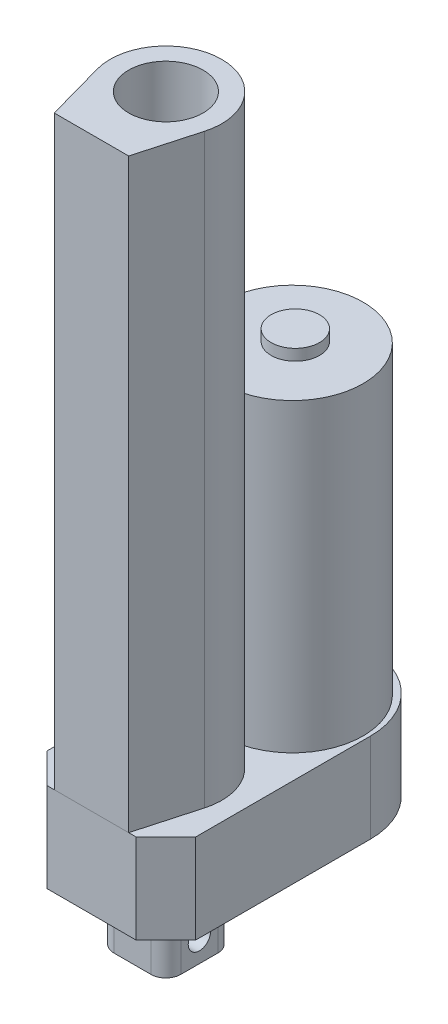
SolidWorks part; units mm, degrees
ref_plane "前视基准面" through (0, 0, 0) normal (0, 0, 1) x (1, 0, 0)
ref_plane "上视基准面" through (0, 0, 0) normal (0, 1, 0) x (1, 0, 0)
ref_plane "右视基准面" through (0, 0, 0) normal (1, 0, 0) x (0, 0, -1)
sketch "草图1" plane through (0, 0, 0) normal (0, 1, 0) x (1, 0, 0)
  line L0 (0, 8) -> (8, 0)
  line L1 (8, 0) -> (32, 0)
  line L2 (0, 8) -> (0, 55)
  line L4 (40, 8) -> (40, 55)
  line L5 (32, 0) -> (40, 8)
  arc A0 (40, 55) -> (0, 55) centre (20, 55) ccw
  point P0 (0, 0)
  point P4 (40, 0)
  dimension "D3" = 20
  dimension "D1" = 55
  dimension "D2" = 40
extrude "凸台-拉伸1" add sketch "草图1" along normal blind 24
sketch "草图2" plane through (0, 0, 0) normal (0, -1, 0) x (1, 0, 0)
  line L0 (8, 0) -> (32, 0) construction
  line L1 (15, -11) -> (25, -11)
  line L2 (11, -15) -> (11, -25)
  line L3 (15, -29) -> (25, -29)
  line L4 (29, -15) -> (29, -25)
  line L5 (0, -55) -> (0, -8) construction
  arc A0 (11, -25) -> (15, -29) centre (15, -25) ccw
  arc A1 (25, -29) -> (29, -25) centre (25, -25) ccw
  arc A2 (25, -11) -> (29, -15) centre (25, -15) cw
  arc A3 (15, -11) -> (11, -15) centre (15, -15) ccw
  point P12 (20, -29)
  dimension "D1" = 4
  dimension "D2" = 4
  dimension "D3" = 4
  dimension "D4" = 4
  dimension "D5" = 18
  dimension "D6" = 18
  dimension "D7" = 11
  dimension "D8" = 11
extrude "凸台-拉伸2" add sketch "草图2" along normal blind 17
sketch "草图3" plane through (29, 0, 0) normal (1, 0, 0) x (0, 0, -1)
  line L0 (25, -17) -> (15, -17) construction
  line L1 (8, 24) -> (55, 24) construction
  line L3 (11, -17) -> (11, 0) construction
  circle A0 centre (20, -11) radius 3
  dimension "D1" = 6
  dimension "D4" = 35
  dimension "D2" = 6
  dimension "D3" = 9
extrude "切除-拉伸1" cut sketch "草图3" against normal through all both and the other way through all
sketch "草图4" plane through (0, 24, 0) normal (0, 1, 0) x (1, 0, 0)
  line L0 (8, 0) -> (32, 0) construction
  line L2 (0, 55) -> (0, 8) construction
  circle A0 centre (20, 54) radius 19
  dimension "D1" = 38
  dimension "D2" = 54
  dimension "D3" = 20
extrude "凸台-拉伸3" add sketch "草图4" along normal blind 82
sketch "草图5" plane through (0, 106, 0) normal (0, 1, 0) x (1, 0, 0)
  circle A0 centre (20.0766, 54.7074) radius 6.5
  dimension "D1" = 13
extrude "凸台-拉伸4" add sketch "草图5" along normal blind 3
sketch "草图6" plane through (0, 24, 0) normal (0, 1, 0) x (1, 0, 0)
  line L0 (0, 55) -> (0, 8) construction
  line L1 (8, 0) -> (32, 0) construction
  line L2 (10, 0) -> (5.5501, 15.9749)
  line L3 (30, 0) -> (34.4499, 15.9749)
  line L4 (30, 0) -> (10, 0)
  arc A0 (34.4499, 15.9749) -> (5.5501, 15.9749) centre (20, 20) ccw
  circle A1 centre (20, 20) radius 10
  dimension "D1" = 30
  dimension "D2" = 20
  dimension "D3" = 20
  dimension "D4" = 20
  dimension "D5" = 20
extrude "凸台-拉伸7" add sketch "草图6" along normal blind 157.5 separate body
